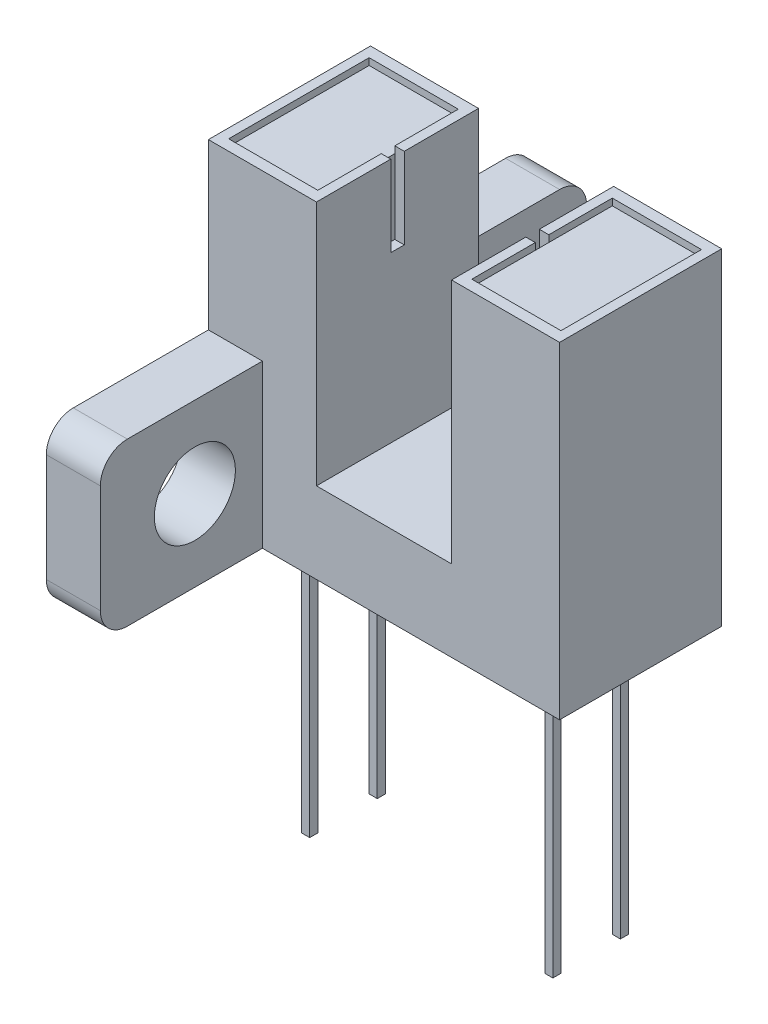
SolidWorks part; units mm, degrees
ref_plane "Front Plane" through (0, 0, 0) normal (0, 0, 1) x (1, 0, 0)
ref_plane "Top Plane" through (0, 0, 0) normal (0, 1, 0) x (1, 0, 0)
ref_plane "Right Plane" through (0, 0, 0) normal (1, 0, 0) x (0, 0, -1)
sketch "Sketch1" plane through (0, 0, 0) normal (0, 0, 1) x (1, 0, 0)
  line L0 (-9, 12.1) -> (-13, 12.1)
  line L1 (0, 0) -> (-13, 0)
  line L2 (0, 0) -> (0, 12.1)
  line L3 (0, 12.1) -> (-4, 12.1)
  line L4 (-13, 0) -> (-13, 12.1)
  line L6 (-9, 12.1) -> (-9, 3)
  line L7 (-9, 3) -> (-4, 3)
  line L8 (-4, 12.1) -> (-4, 3)
  dimension "D1" = 12.1
  dimension "D2" = 3
  dimension "D3" = 13
  dimension "D4" = 5
extrude "Boss-Extrude1" add sketch "Sketch1" along normal mid plane 6
sketch "Sketch3" plane through (-13, 0, 0) normal (-1, 0, 0) x (0, 0, 1)
  line L0 (0, 0) -> (0, 10.2274) construction
  line L1 (-9, 0) -> (9, 0)
  line L2 (-9, 0) -> (-9, 6)
  line L3 (-9, 6) -> (9, 6)
  line L4 (9, 0) -> (9, 6)
  line L5 (3, 0) -> (-3, 0) construction
  dimension "D1" = 18
  dimension "D2" = 6
extrude "Boss-Extrude2" add sketch "Sketch3" against normal blind 2
sketch "Sketch4" plane through (-13, 0, 0) normal (-1, 0, 0) x (0, 0, 1)
  line L0 (0, 0) -> (0, 4.4557) construction
  line L1 (-9, 3) -> (9, 3) construction
  line L2 (-9, 6) -> (-9, 0) construction
  line L3 (9, 0) -> (9, 6) construction
  circle A0 centre (-5.5, 3) radius 1.5
  circle A1 centre (5.5, 3) radius 1.5
  dimension "D1" = 3
  dimension "D2" = 11
extrude "Cut-Extrude1" cut sketch "Sketch4" against normal through all
fillet "Fillet1" radius 1 4 edges at (-12, 0, 9) (-12, 6, 9) (-12, 0, -9) (-12, 6, -9)
ref_plane "Plane1" through (-6.5, 0, 0) normal (1, 0, 0) x (0, 0, -1)
sketch "Sketch5" plane through (0, 12.1, 0) normal (0, 1, 0) x (1, 0, 0)
  line L0 (-13, -3) -> (-13, 3) construction
  line L5 (-9.35, 2.6) -> (-12.65, 2.6)
  line L6 (-9.35, 2.6) -> (-9.35, -2.6)
  line L7 (-9.35, -2.6) -> (-12.65, -2.6)
  line L8 (-12.65, 2.6) -> (-12.65, -2.6)
  line L9 (-9, -3) -> (-9, 3) construction
  line L10 (-9, 3) -> (-13, 3) construction
  line L11 (-9, -3) -> (-13, -3) construction
  dimension "D1" = 0.35
  dimension "D2" = 0.35
  dimension "D3" = 0.4
  dimension "D4" = 0.4
extrude "Cut-Extrude2" cut sketch "Sketch5" against normal blind 0.25
sketch "Sketch6" plane through (-9, 0, 0) normal (1, 0, 0) x (0, 0, -1)
  line L0 (-3, 12.1) -> (3, 12.1) construction
  line L1 (0.25, 12.1) -> (-0.25, 12.1)
  line L2 (0.25, 12.1) -> (0.25, 9.1)
  line L3 (0.25, 9.1) -> (-0.25, 9.1)
  line L4 (-0.25, 12.1) -> (-0.25, 9.1)
  line L5 (0, 12.1) -> (0, 9.3097) construction
  dimension "D1" = 0.5
  dimension "D2" = 3
extrude "Cut-Extrude3" cut sketch "Sketch6" against normal up to surface (0.35 mm away) up to face at (-9.35, 11.975, 0)
mirror "Mirror1" about plane through (-6.5, 0, 0) normal (1, 0, 0) of "Cut-Extrude3", "Cut-Extrude2"
sketch "Sketch7" plane through (0, 0, 0) normal (0, -1, 0) x (1, 0, 0)
  line L0 (-6.5, -3.3) -> (-6.5, 3.3) construction
  line L1 (-12.5, 2.5) -> (-0.5, 2.5)
  line L2 (-12.5, 2.5) -> (-12.5, -2.5)
  line L3 (-12.5, -2.5) -> (-0.5, -2.5)
  line L4 (-0.5, 2.5) -> (-0.5, -2.5)
  line L5 (-12.5, 2.5) -> (-0.5, -2.5) construction
  line L6 (-12.5, -2.5) -> (-0.5, 2.5) construction
  point P0 (-6.5, 0)
  dimension "D1" = 12
  dimension "D2" = 5
extrude "Cut-Extrude4" cut sketch "Sketch7" against normal blind 2
sketch "Sketch8" plane through (0, 2, 0) normal (0, -1, 0) x (1, 0, 0)
  line L0 (-6.5, -3.3) -> (-6.5, 3.3) construction
  line L1 (-11.15, 1.4) -> (-10.85, 1.4)
  line L2 (-11.15, 1.4) -> (-11.15, 1.1)
  line L3 (-11.15, 1.1) -> (-10.85, 1.1)
  line L4 (-10.85, 1.4) -> (-10.85, 1.1)
  line L5 (-11.15, 1.4) -> (-10.85, 1.1) construction
  line L6 (-11.15, 1.1) -> (-10.85, 1.4) construction
  point P0 (-11, 1.25)
  dimension "D1" = 0.3
  dimension "D2" = 4.5
  dimension "D3" = 1.25
extrude "Boss-Extrude3" add sketch "Sketch8" along normal blind 12
pattern_linear "LPattern1" count 2 spacing 9 along (1, 0, 0) count 2 spacing 2.5 along (0, 0, -1) of "Boss-Extrude3"
